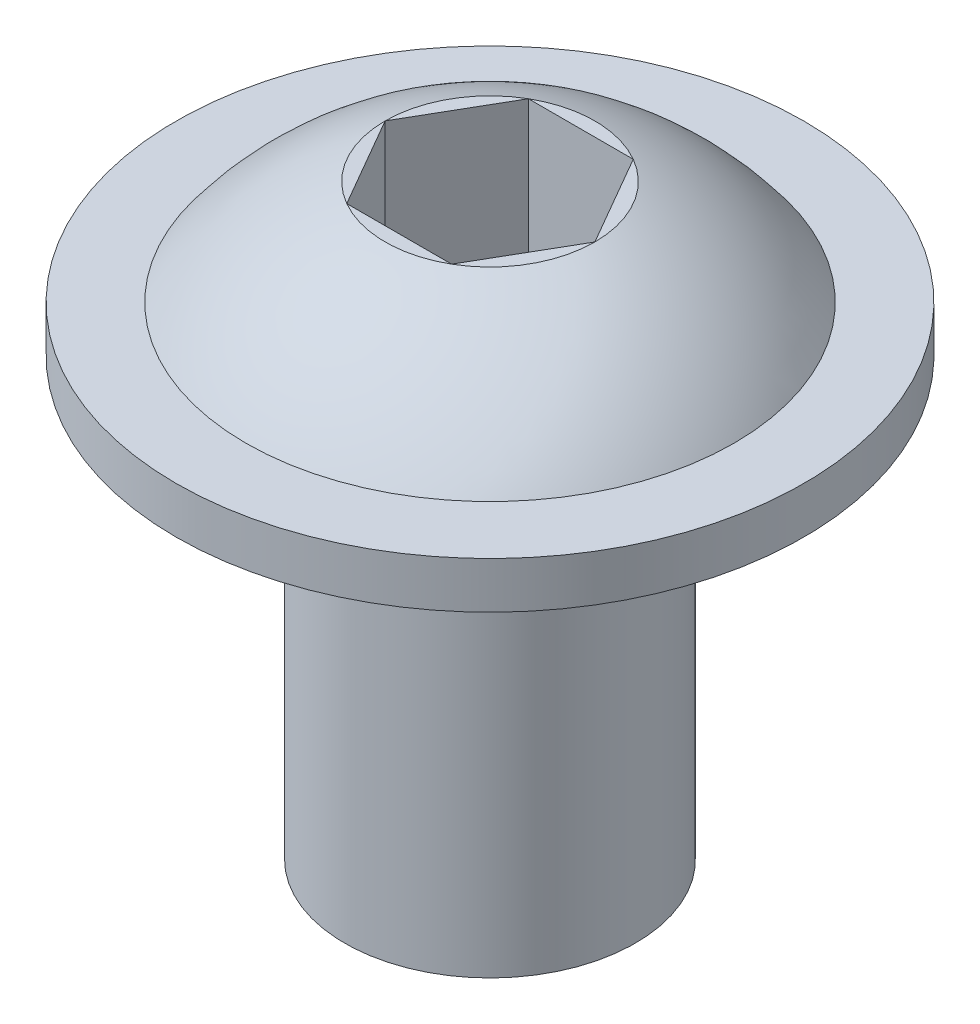
SolidWorks part; units mm, degrees
ref_plane "Front"
ref_plane "Top" through (0, 0, 0) normal (0, 1, 0) x (1, 0, 0)
ref_plane "Right" through (0, 0, 0) normal (1, 0, 0) x (0, 0, -1)
sketch "Sketch1" plane through (0, 0, 0) normal (0, 0, 1) x (1, 0, 0)
  line L0 (0, 0) -> (3.175, 0)
  line L1 (3.175, 0) -> (3.175, 9.525)
  line L2 (3.175, 9.525) -> (6.858, 9.525)
  line L3 (6.858, 9.525) -> (6.858, 10.541)
  line L4 (6.858, 10.541) -> (5.334, 10.541)
  line L5 (0, 0) -> (0, 12.827)
  line L6 (0, 0) -> (0, 30.7805) construction
  line L8 (2.2914, 12.827) -> (0, 12.827)
  arc A0 (5.334, 10.541) -> (2.2914, 12.827) centre (0, 6.6094) ccw
  dimension "MajorDia" = 6.35
  dimension "D2" = 4.5827
  dimension "Length" = 9.525
  dimension "FlangeThick" = 1.016
  dimension "FlangeDiam" = 13.716
  dimension "HeadHeight" = 3.302
  dimension "HeadDiam" = 10.668
revolve "Screw revolve" add sketch "Sketch1" angle 360 about L6
sketch "Sketch2" plane through (0, 12.827, 0) normal (0, 1, 0) x (-1, 0, 0)
  line L1 (-2.2914, 0) -> (-1.1457, -1.9844)
  line L2 (-1.1457, -1.9844) -> (1.1457, -1.9844)
  line L3 (1.1457, -1.9844) -> (2.2914, 0)
  line L4 (2.2914, 0) -> (1.1457, 1.9844)
  line L5 (1.1457, 1.9844) -> (-1.1457, 1.9844)
  line L6 (-1.1457, 1.9844) -> (-2.2914, 0)
  circle A0 centre (0, 0) radius 1.9844 construction
  dimension "D1" = 4.5827
  dimension "HexWidth" = 3.9688
extrude "Hex Cut" cut sketch "Sketch2" against normal blind 3.175
equation "\"D2@Sketch1\" = \"D1@Sketch2\""
